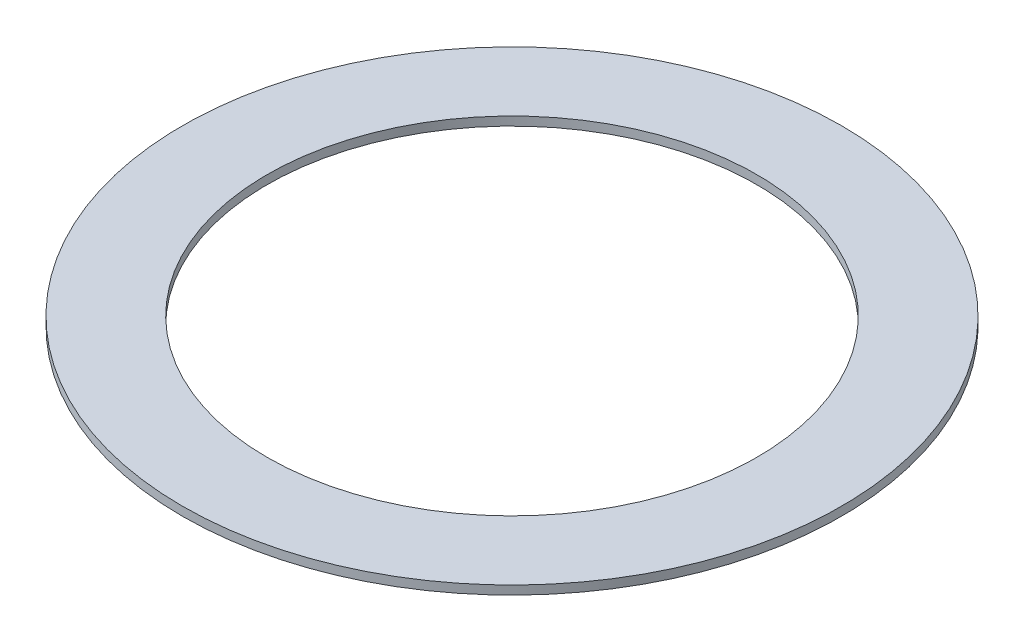
SolidWorks part; units mm, degrees
ref_plane "Front Plane" through (0, 0, 0) normal (0, 0, 1) x (1, 0, 0)
ref_plane "Top Plane" through (0, 0, 0) normal (0, 1, 0) x (1, 0, 0)
ref_plane "Right Plane" through (0, 0, 0) normal (1, 0, 0) x (0, 0, -1)
sketch "Sketch1" plane through (0, 0, 0) normal (0, 1, 0) x (1, 0, 0)
  circle A0 centre (0, 0) radius 88.9
  circle A1 centre (0, 0) radius 119.634
  dimension "D1" = 177.8
  dimension "D2" = 239.268
extrude "Boss-Extrude1" add sketch "Sketch1" along normal blind 3.175
equation "\"2x3.5\"=3.60815"
